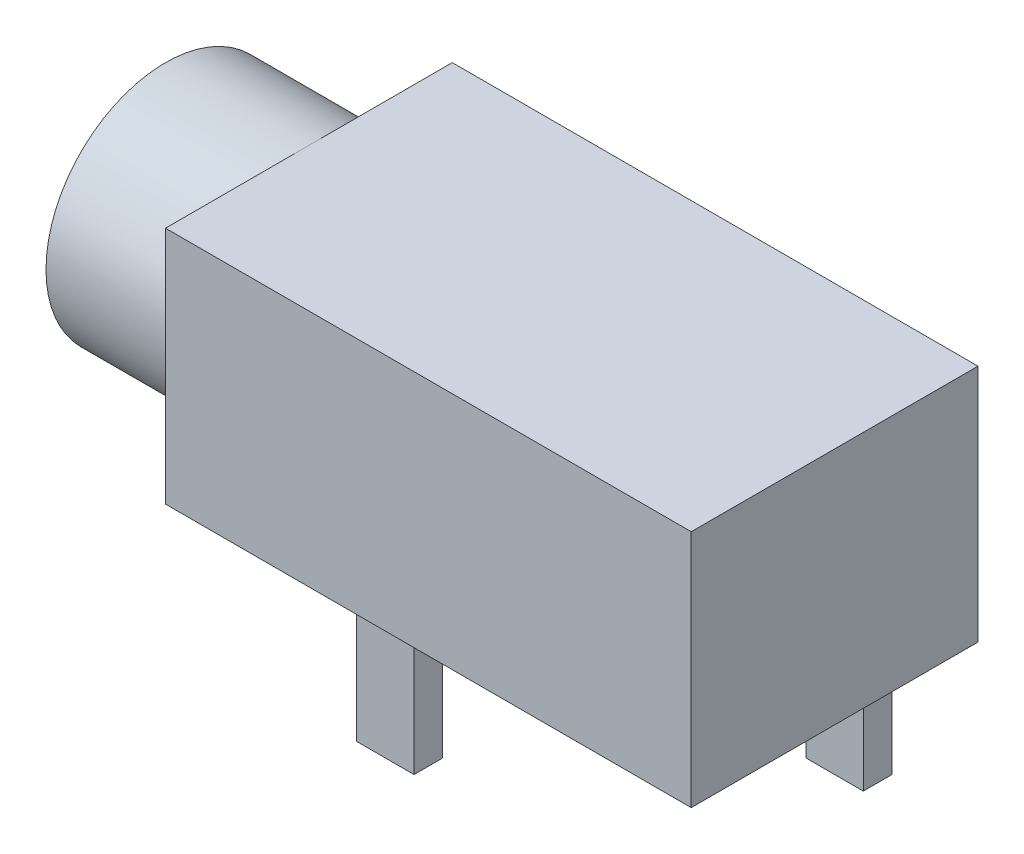
SolidWorks part; units mm, degrees
ref_plane "Front" through (0, 0, 0) normal (0, 0, 1) x (1, 0, 0)
ref_plane "Top" through (0, 0, 0) normal (0, 1, 0) x (1, 0, 0)
ref_plane "Right" through (0, 0, 0) normal (1, 0, 0) x (0, 0, -1)
sketch "Sketch1" plane through (0, 0, 0) normal (0, 1, 0) x (1, 0, 0)
  line L1 (0, 0) -> (11, 0)
  line L2 (0, 0) -> (0, -6)
  line L3 (0, -6) -> (11, -6)
  line L4 (11, 0) -> (11, -6)
  dimension "D1" = 11
  dimension "D2" = 6
extrude "Boss-Extrude1" add sketch "Sketch1" along normal blind 5
sketch "Sketch2" plane through (0, 0, 0) normal (-1, 0, 0) x (0, 0, 1)
  line L0 (0, 0) -> (6, 0) construction
  line L1 (6, 5) -> (6, 0) construction
  circle A0 centre (3, 2.5) radius 2.5
  dimension "D3" = 5
  dimension "D1" = 2.5
  dimension "D2" = 3
extrude "Boss-Extrude2" add sketch "Sketch2" along normal blind 3
sketch "Sketch3" plane through (0, 0, 0) normal (0, -1, 0) x (-1, 0, 0)
  line L0 (0, 0) -> (0, -3) construction
  line L1 (-1.5, -1.1) -> (-2.7, -1.1)
  line L2 (-1.5, -1.1) -> (-1.5, -0.5)
  line L3 (-1.5, -0.5) -> (-2.7, -0.5)
  line L4 (-2.7, -1.1) -> (-2.7, -0.5)
  line L5 (-8.5, -1.1) -> (-9.7, -1.1)
  line L6 (-8.5, -1.1) -> (-8.5, -0.5)
  line L7 (-8.5, -0.5) -> (-9.7, -0.5)
  line L8 (-9.7, -1.1) -> (-9.7, -0.5)
  line L9 (-3.5, -5.5) -> (-4.7, -5.5)
  line L10 (-3.5, -5.5) -> (-3.5, -4.9)
  line L11 (-3.5, -4.9) -> (-4.7, -4.9)
  line L12 (-4.7, -5.5) -> (-4.7, -4.9)
  line L13 (0, -3) -> (0, -6) construction
  line L14 (-11, 0) -> (0, 0) construction
  line L15 (0, -6) -> (-11, -6) construction
  dimension "D1" = 1.2
  dimension "D2" = 1.2
  dimension "D3" = 1.2
  dimension "D4" = 0.6
  dimension "D5" = 0.6
  dimension "D6" = 0.6
  dimension "D7" = 1.5
  dimension "D8" = 8.5
  dimension "D9" = 3.5
  dimension "D10" = 0.5
  dimension "D11" = 0.5
  dimension "D12" = 0.5
extrude "Boss-Extrude3" add sketch "Sketch3" along normal blind 2.8
